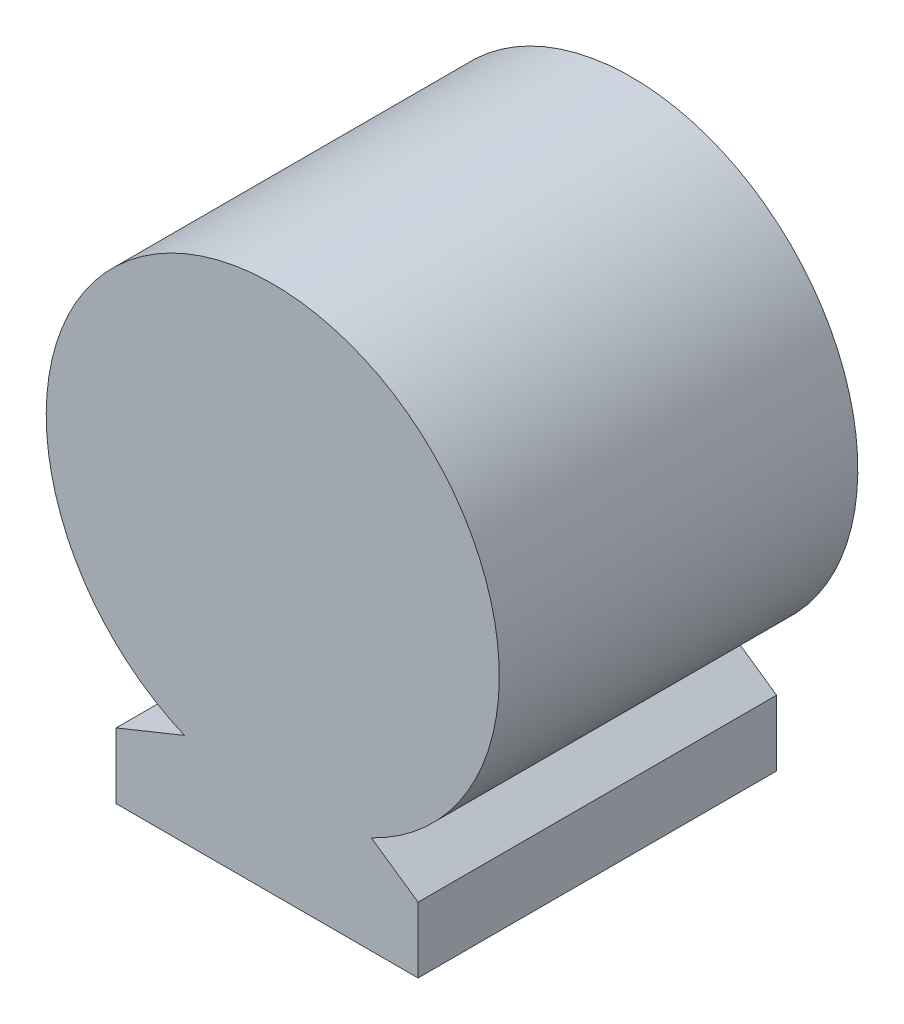
SolidWorks part; units mm, degrees
ref_plane "Płaszczyzna przednia" through (0, 0, 0) normal (0, 0, 1) x (1, 0, 0)
ref_plane "Płaszczyzna górna" through (0, 0, 0) normal (0, 1, 0) x (1, 0, 0)
ref_plane "Płaszczyzna prawa" through (0, 0, 0) normal (1, 0, 0) x (0, 0, -1)
sketch "Szkic1" plane through (0, 0, 0) normal (0, 0, 1) x (1, 0, 0)
  line L0 (-41.5, -80) -> (38.5, -80)
  line L1 (-1.5, -80) -> (-1.5, 60) construction
  line L2 (-41.5, -80) -> (-41.5, -62.6095)
  line L3 (-41.5, -62.6095) -> (-23.3882, -55.2743)
  line L4 (38.5, -80) -> (38.5, -62.6095)
  line L5 (38.5, -62.6095) -> (26.1209, -54.0365)
  arc A0 (26.1209, -54.0365) -> (-23.3882, -55.2743) centre (0, 0) ccw
  dimension "D1" = 80
  dimension "D2" = 140
extrude "Dodanie-wyciągnięcie1" add sketch "Szkic1" along normal blind 95
